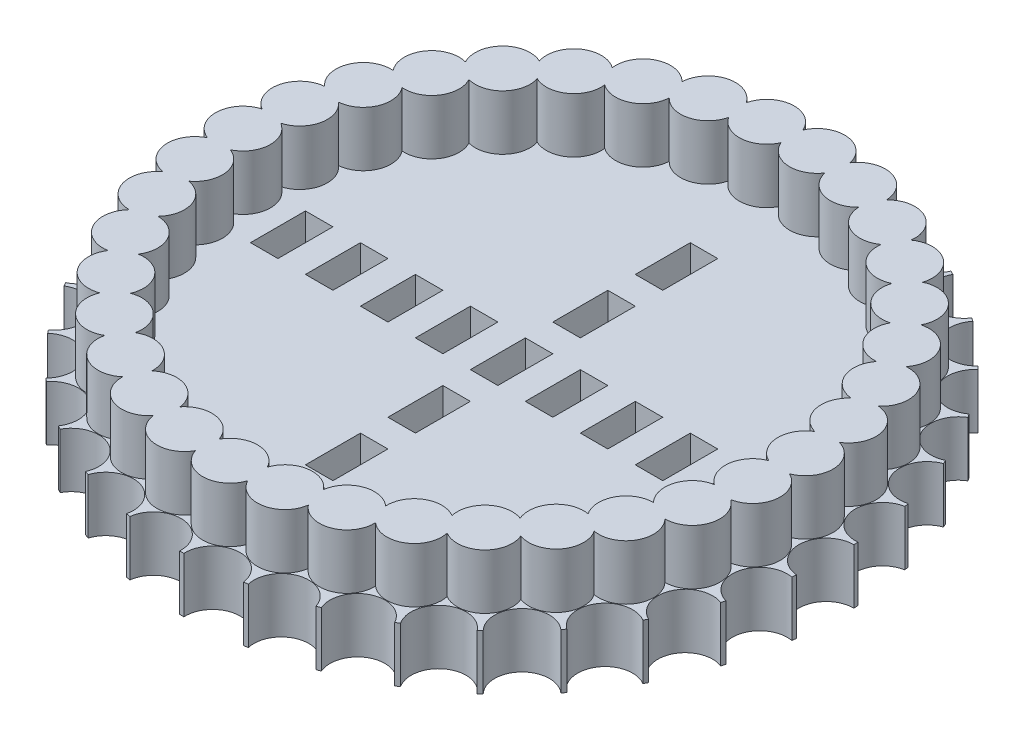
SolidWorks part; units mm, degrees
ref_plane "Front Plane" through (0, 0, 0) normal (0, 0, 1) x (1, 0, 0)
ref_plane "Top Plane" through (0, 0, 0) normal (0, 1, 0) x (1, 0, 0)
ref_plane "Right Plane" through (0, 0, 0) normal (1, 0, 0) x (0, 0, -1)
sketch "Sketch1" plane through (0, 0, 0) normal (0, 1, 0) x (1, 0, 0)
  circle A0 centre (0, 0) radius 76.2
  dimension "D1" = 152.4
extrude "Boss-Extrude1" add sketch "Sketch1" along normal blind 12.7
sketch "Sketch2" plane through (0, 12.7, 0) normal (0, 1, 0) x (1, 0, 0)
  line L0 (0, 0) -> (0, 76.2) construction
  circle A0 centre (0, 0) radius 76.2 construction
  circle A1 centre (0, 76.2) radius 6.35
  dimension "D1" = 12.7
  dimension "D2" = 76.2
extrude "Cut-Extrude1" cut sketch "Sketch2" against normal through all
pattern_circular "CirPattern1" count 35 over 360 about axis through (0, 0, 0) along (0, 1, 0) of "Cut-Extrude1"
sketch "Sketch3" plane through (0, 12.7, 0) normal (0, 1, 0) x (1, 0, 0)
  line L0 (6.8305, 75.8932) -> (6.3986, 71.0944) construction
  line L1 (5.2602, 58.4456) -> (0, 0) construction
  arc A0 (7.3163, 75.848) -> (6.3445, 75.9354) centre (0, 0) ccw construction
  arc A1 (12.0147, 66.2067) -> (0, 67.288) centre (5.8294, 64.77) ccw
  arc A2 (23.6433, 62.9974) -> (12.0147, 66.2067) centre (17.3009, 62.6882) ccw
  arc A3 (34.512, 57.7633) -> (23.6433, 62.9974) centre (28.2162, 58.5916) ccw
  arc A4 (44.2714, 50.6727) -> (34.512, 57.7633) centre (38.2247, 52.6118) ccw
  arc A5 (52.6079, 41.9534) -> (44.2714, 50.6727) centre (47.0047, 44.941) ccw
  arc A6 (59.2535, 31.8857) -> (52.6079, 41.9534) centre (54.2738, 35.8258) ccw
  arc A7 (63.9947, 20.7931) -> (59.2535, 31.8857) centre (59.7985, 25.5591) ccw
  arc A8 (66.6791, 9.0323) -> (63.9947, 20.7931) centre (63.4013, 14.4709) ccw
  arc A9 (67.2203, -3.0189) -> (66.6791, 9.0323) centre (64.9663, 2.9176) ccw
  arc A10 (65.601, -14.973) -> (67.2203, -3.0189) centre (64.4432, -8.7294) ccw
  arc A11 (61.8732, -26.4459) -> (65.601, -14.973) centre (61.8489, -20.0959) ccw
  arc A12 (56.1568, -37.0688) -> (61.8732, -26.4459) centre (57.2667, -30.8165) ccw
  arc A13 (48.6355, -46.5003) -> (56.1568, -37.0688) centre (50.8439, -40.5467) ccw
  arc A14 (39.5509, -54.4372) -> (48.6355, -46.5003) centre (42.7869, -48.9736) ccw
  arc A15 (29.1952, -60.6244) -> (39.5509, -54.4372) centre (33.3548, -55.8265) ccw
  arc A16 (17.9011, -64.8632) -> (29.1952, -60.6244) centre (22.8505, -60.885) ccw
  arc A17 (6.0317, -67.0172) -> (17.9011, -64.8632) centre (11.6119, -63.9867) ccw
  arc A18 (-6.0317, -67.0172) -> (6.0317, -67.0172) centre (0, -65.0318) ccw
  arc A19 (-17.9011, -64.8632) -> (-6.0317, -67.0172) centre (-11.6119, -63.9867) ccw
  arc A20 (-29.1952, -60.6244) -> (-17.9011, -64.8632) centre (-22.8505, -60.885) ccw
  arc A21 (-39.5509, -54.4372) -> (-29.1952, -60.6244) centre (-33.3548, -55.8265) ccw
  arc A22 (-48.6355, -46.5003) -> (-39.5509, -54.4372) centre (-42.7869, -48.9736) ccw
  arc A23 (-56.1568, -37.0688) -> (-48.6355, -46.5003) centre (-50.8439, -40.5467) ccw
  arc A24 (-61.8732, -26.4459) -> (-56.1568, -37.0688) centre (-57.2667, -30.8165) ccw
  arc A25 (-65.601, -14.973) -> (-61.8732, -26.4459) centre (-61.8489, -20.0959) ccw
  arc A26 (-67.2203, -3.0189) -> (-65.601, -14.973) centre (-64.4432, -8.7294) ccw
  arc A27 (-66.6791, 9.0323) -> (-67.2203, -3.0189) centre (-64.9663, 2.9176) ccw
  arc A28 (-63.9947, 20.7931) -> (-66.6791, 9.0323) centre (-63.4013, 14.4709) ccw
  arc A29 (-59.2535, 31.8857) -> (-63.9947, 20.7931) centre (-59.7985, 25.5591) ccw
  arc A30 (-54.8188, 29.4993) -> (-48.6705, 38.8135) centre (-54.2738, 35.8258) ccw
  arc A31 (-44.2714, 50.6727) -> (-52.6079, 41.9534) centre (-47.0047, 44.941) ccw
  arc A32 (-34.512, 57.7633) -> (-44.2714, 50.6727) centre (-38.2247, 52.6118) ccw
  arc A33 (-23.6433, 62.9974) -> (-34.512, 57.7633) centre (-28.2162, 58.5916) ccw
  arc A34 (-12.0147, 66.2067) -> (-23.6433, 62.9974) centre (-17.3009, 62.6882) ccw
  arc A35 (0, 67.288) -> (-12.0147, 66.2067) centre (-5.8294, 64.77) ccw
  arc A36 (-59.2051, 19.2369) -> (-54.8188, 29.4993) centre (-59.7985, 25.5591) ccw
  arc A37 (-61.6886, 8.3563) -> (-59.2051, 19.2369) centre (-63.4013, 14.4709) ccw
  arc A38 (-62.1893, -2.7929) -> (-61.6886, 8.3563) centre (-64.9663, 2.9176) ccw
  arc A39 (-60.6912, -13.8524) -> (-62.1893, -2.7929) centre (-64.4432, -8.7294) ccw
  arc A40 (-57.2424, -24.4666) -> (-60.6912, -13.8524) centre (-61.8489, -20.0959) ccw
  arc A41 (-51.9538, -34.2944) -> (-57.2424, -24.4666) centre (-57.2667, -30.8165) ccw
  arc A42 (-44.9954, -43.02) -> (-51.9538, -34.2944) centre (-50.8439, -40.5467) ccw
  arc A43 (-36.5908, -50.3629) -> (-44.9954, -43.02) centre (-42.7869, -48.9736) ccw
  arc A44 (-27.0101, -56.0871) -> (-36.5908, -50.3629) centre (-33.3548, -55.8265) ccw
  arc A45 (-16.5613, -60.0086) -> (-27.0101, -56.0871) centre (-22.8505, -60.885) ccw
  arc A46 (-5.5802, -62.0014) -> (-16.5613, -60.0086) centre (-11.6119, -63.9867) ccw
  arc A47 (5.5802, -62.0014) -> (-5.5802, -62.0014) centre (0, -65.0318) ccw
  arc A48 (16.5613, -60.0086) -> (5.5802, -62.0014) centre (11.6119, -63.9867) ccw
  arc A49 (27.0101, -56.0871) -> (16.5613, -60.0086) centre (22.8505, -60.885) ccw
  arc A50 (36.5908, -50.3629) -> (27.0101, -56.0871) centre (33.3548, -55.8265) ccw
  arc A51 (44.9954, -43.02) -> (36.5908, -50.3629) centre (42.7869, -48.9736) ccw
  arc A52 (51.9538, -34.2944) -> (44.9954, -43.02) centre (50.8439, -40.5467) ccw
  arc A53 (57.2424, -24.4666) -> (51.9538, -34.2944) centre (57.2667, -30.8165) ccw
  arc A54 (60.6912, -13.8524) -> (57.2424, -24.4666) centre (61.8489, -20.0959) ccw
  arc A55 (62.1893, -2.7929) -> (60.6912, -13.8524) centre (64.4432, -8.7294) ccw
  arc A56 (61.6886, 8.3563) -> (62.1893, -2.7929) centre (64.9663, 2.9176) ccw
  arc A57 (59.2051, 19.2369) -> (61.6886, 8.3563) centre (63.4013, 14.4709) ccw
  arc A58 (54.8188, 29.4993) -> (59.2051, 19.2369) centre (59.7985, 25.5591) ccw
  arc A59 (48.6705, 38.8135) -> (54.8188, 29.4993) centre (54.2738, 35.8258) ccw
  arc A60 (40.958, 46.8802) -> (48.6705, 38.8135) centre (47.0047, 44.941) ccw
  arc A61 (31.929, 53.4401) -> (40.958, 46.8802) centre (38.2247, 52.6118) ccw
  arc A62 (21.8738, 58.2825) -> (31.929, 53.4401) centre (28.2162, 58.5916) ccw
  arc A63 (11.1155, 61.2515) -> (21.8738, 58.2825) centre (17.3009, 62.6882) ccw
  arc A64 (0, 62.252) -> (11.1155, 61.2515) centre (5.8294, 64.77) ccw
  arc A65 (-11.1155, 61.2515) -> (0, 62.252) centre (-5.8294, 64.77) ccw
  arc A66 (-21.8738, 58.2825) -> (-11.1155, 61.2515) centre (-17.3009, 62.6882) ccw
  arc A67 (-31.929, 53.4401) -> (-21.8738, 58.2825) centre (-28.2162, 58.5916) ccw
  arc A68 (-40.958, 46.8802) -> (-31.929, 53.4401) centre (-38.2247, 52.6118) ccw
  arc A69 (-52.6079, 41.9534) -> (-59.2535, 31.8857) centre (-54.2738, 35.8258) ccw
  arc A70 (-48.6705, 38.8135) -> (-40.958, 46.8802) centre (-47.0047, 44.941) ccw
  point P79 (0, 0)
  dimension "D1" = 12.7
  dimension "D2" = 64.77
  dimension "D3" = 35
extrude "Boss-Extrude2" add sketch "Sketch3" along normal blind 12.7
sketch "Sketch4" plane through (0, 12.7, 0) normal (0, 1, 0) x (1, 0, 0)
  line L0 (0, 0) -> (0, 94.297) construction
  line L1 (0, 0) -> (132.1988, 0) construction
  line L2 (0, 0) -> (-121.2439, 0) construction
  line L3 (0, 0) -> (0, -102.204) construction
  line L4 (9.525, -6.35) -> (15.875, -6.35)
  line L5 (-3.175, 6.35) -> (3.175, 6.35)
  line L6 (-3.175, 6.35) -> (-3.175, -6.35)
  line L7 (-3.175, -6.35) -> (3.175, -6.35)
  line L8 (3.175, 6.35) -> (3.175, -6.35)
  line L9 (-3.175, 6.35) -> (3.175, -6.35) construction
  line L10 (-3.175, -6.35) -> (3.175, 6.35) construction
  line L11 (15.875, 6.35) -> (15.875, -6.35)
  line L12 (9.525, 6.35) -> (9.525, -6.35)
  line L13 (9.525, 6.35) -> (15.875, 6.35)
  line L14 (22.225, -6.35) -> (28.575, -6.35)
  line L15 (28.575, 6.35) -> (28.575, -6.35)
  line L16 (22.225, 6.35) -> (22.225, -6.35)
  line L17 (22.225, 6.35) -> (28.575, 6.35)
  line L18 (34.925, -6.35) -> (41.275, -6.35)
  line L19 (41.275, 6.35) -> (41.275, -6.35)
  line L20 (34.925, 6.35) -> (34.925, -6.35)
  line L21 (34.925, 6.35) -> (41.275, 6.35)
  line L22 (47.625, -6.35) -> (53.975, -6.35)
  line L23 (53.975, 6.35) -> (53.975, -6.35)
  line L24 (47.625, 6.35) -> (47.625, -6.35)
  line L25 (47.625, 6.35) -> (53.975, 6.35)
  line L26 (-3.175, 12.7) -> (3.175, 12.7)
  line L27 (-3.175, 25.4) -> (-3.175, 12.7)
  line L28 (-3.175, 25.4) -> (3.175, 25.4)
  line L29 (3.175, 25.4) -> (3.175, 12.7)
  line L30 (-3.175, 31.75) -> (3.175, 31.75)
  line L31 (-3.175, 44.45) -> (-3.175, 31.75)
  line L32 (-3.175, 44.45) -> (3.175, 44.45)
  line L33 (3.175, 44.45) -> (3.175, 31.75)
  line L34 (-3.175, -25.4) -> (3.175, -25.4)
  line L35 (3.175, -12.7) -> (3.175, -25.4)
  line L36 (-3.175, -12.7) -> (-3.175, -25.4)
  line L37 (-3.175, -12.7) -> (3.175, -12.7)
  line L38 (-3.175, -44.45) -> (3.175, -44.45)
  line L39 (3.175, -31.75) -> (3.175, -44.45)
  line L40 (-3.175, -31.75) -> (-3.175, -44.45)
  line L41 (-3.175, -31.75) -> (3.175, -31.75)
  line L42 (-15.875, -6.35) -> (-9.525, -6.35)
  line L43 (-15.875, 6.35) -> (-15.875, -6.35)
  line L44 (-15.875, 6.35) -> (-9.525, 6.35)
  line L45 (-9.525, 6.35) -> (-9.525, -6.35)
  line L46 (-28.575, -6.35) -> (-22.225, -6.35)
  line L47 (-28.575, 6.35) -> (-28.575, -6.35)
  line L48 (-28.575, 6.35) -> (-22.225, 6.35)
  line L49 (-22.225, 6.35) -> (-22.225, -6.35)
  line L50 (-41.275, -6.35) -> (-34.925, -6.35)
  line L51 (-41.275, 6.35) -> (-41.275, -6.35)
  line L52 (-41.275, 6.35) -> (-34.925, 6.35)
  line L53 (-34.925, 6.35) -> (-34.925, -6.35)
  line L54 (-53.975, -6.35) -> (-47.625, -6.35)
  line L55 (-53.975, 6.35) -> (-53.975, -6.35)
  line L56 (-53.975, 6.35) -> (-47.625, 6.35)
  line L57 (-47.625, 6.35) -> (-47.625, -6.35)
  dimension "D1" = 6.35
  dimension "D2" = 12.7
  dimension "D3" = 5
  dimension "D4" = 3
  dimension "D5" = 3
  dimension "D6" = 5
extrude "Cut-Extrude2" cut sketch "Sketch4" against normal through all
